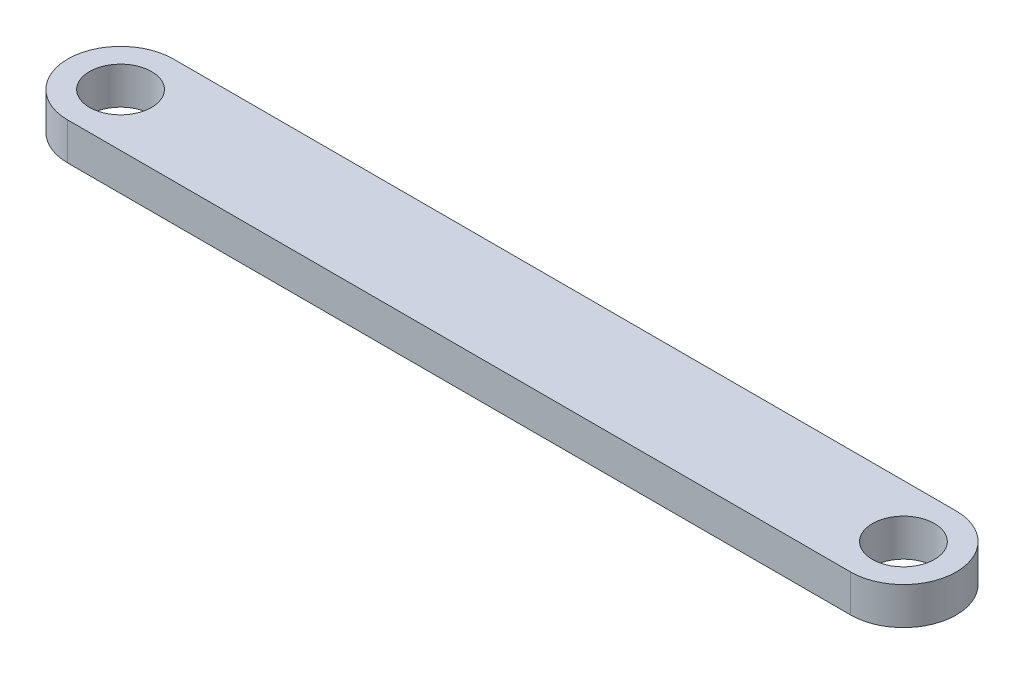
SolidWorks part; units mm, degrees
ref_plane "Front Plane" through (0, 0, 0) normal (0, 0, 1) x (1, 0, 0)
ref_plane "Top Plane" through (0, 0, 0) normal (0, 1, 0) x (1, 0, 0)
ref_plane "Right Plane" through (0, 0, 0) normal (1, 0, 0) x (0, 0, -1)
sketch "Sketch2" plane through (0, 0, 0) normal (0, 1, 0) x (1, 0, 0)
  line L0 (0, -4.25) -> (63, -4.25)
  line L1 (0, 4.25) -> (63, 4.25)
  arc A0 (0, -4.25) -> (0, 4.25) centre (0, 0) cw
  arc A1 (63, 4.25) -> (63, -4.25) centre (63, 0) cw
  dimension "D1" = 63
  dimension "D3" = 8.5
extrude "Boss-Extrude1" add sketch "Sketch2" along normal blind 3 contours L1 A1 L0 A0
sketch "Sketch4" plane through (0, 3, 0) normal (0, 1, 0) x (1, 0, 0)
  circle A0 centre (0, 0) radius 2.5
  circle A1 centre (63, 0) radius 2.5
  arc A2 (63, -4.25) -> (63, 4.25) centre (63, 0) ccw construction
  dimension "D1" = 5
  dimension "D2" = 5
extrude "Cut-Extrude2" cut sketch "Sketch4" against normal through all
